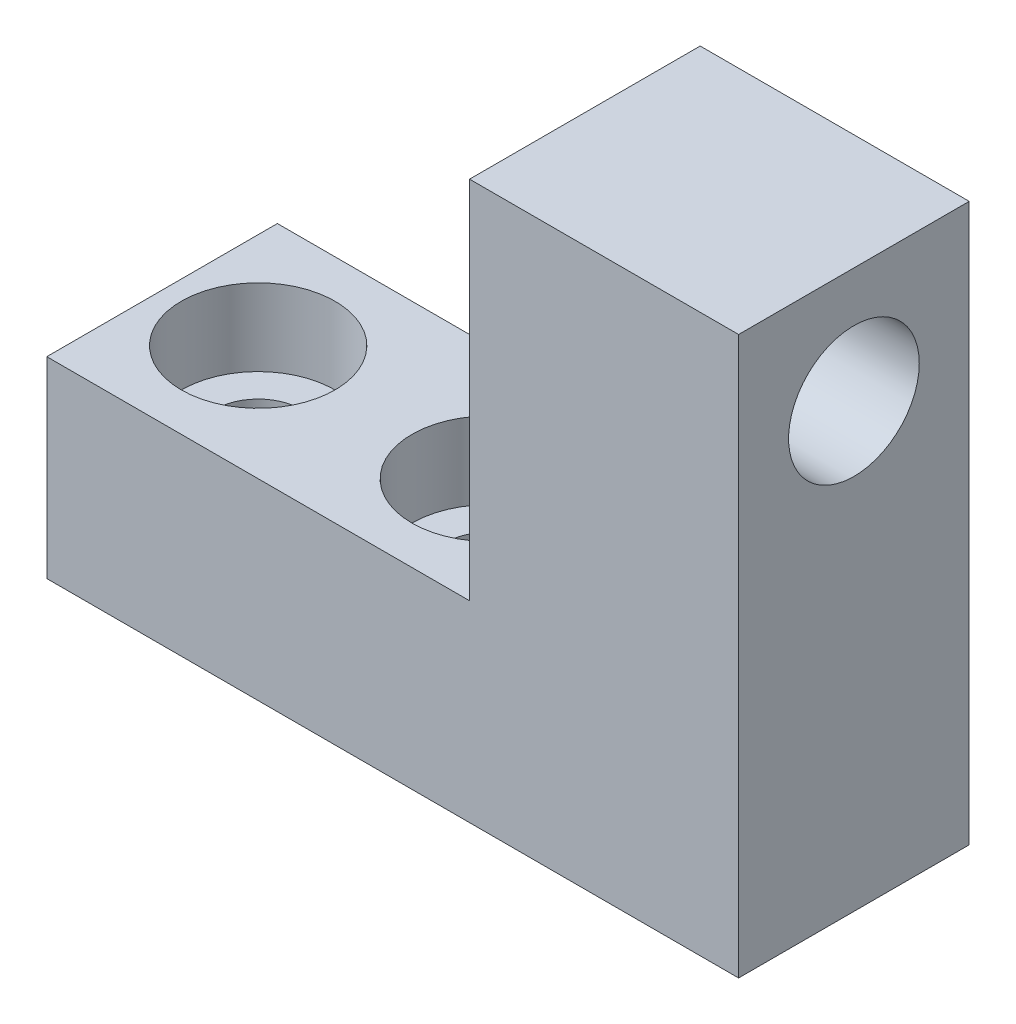
SolidWorks part; units mm, degrees
ref_plane "Front Plane" through (0, 0, 0) normal (0, 0, 1) x (1, 0, 0)
ref_plane "Top Plane" through (0, 0, 0) normal (0, 1, 0) x (1, 0, 0)
ref_plane "Right Plane" through (0, 0, 0) normal (1, 0, 0) x (0, 0, -1)
sketch "Sketch1" plane through (0, 0, 0) normal (0, 0, 1) x (1, 0, 0)
  line L1 (-8.2774, 3.0437) -> (27.7226, 3.0437)
  line L2 (-8.2774, 3.0437) -> (-8.2774, -6.9563)
  line L3 (-8.2774, -6.9563) -> (27.7226, -6.9563)
  line L4 (27.7226, 3.0437) -> (27.7226, -6.9563)
  dimension "D1" = 36
  dimension "D2" = 10
extrude "Boss-Extrude1" add sketch "Sketch1" along normal blind 12
sketch "Sketch2" plane through (0, 3.0437, 0) normal (0, 1, 0) x (1, 0, 0)
  line L0 (27.7226, 0) -> (-8.2774, 0) construction
  line L1 (27.7226, -12) -> (13.7226, -12)
  line L2 (27.7226, -12) -> (27.7226, 0)
  line L3 (27.7226, 0) -> (13.7226, 0)
  line L4 (13.7226, -12) -> (13.7226, 0)
  dimension "D1" = 14
extrude "Boss-Extrude2" add sketch "Sketch2" along normal blind 19
sketch "Sketch3" plane through (0, 3.0437, 0) normal (0, 1, 0) x (1, 0, 0)
  line L0 (-8.2774, -12) -> (-8.2774, 0) construction
  line L1 (27.7226, -12) -> (27.7226, 0) construction
  circle A0 centre (-3.2774, -6) radius 2.25
  circle A1 centre (8.7226, -6) radius 2.25
  point P6 (-8.2774, -6)
  dimension "D1" = 4.5
  dimension "D2" = 5
  dimension "D3" = 19
extrude "Cut-Extrude1" cut sketch "Sketch3" against normal through all
sketch "Sketch4" plane through (0, 3.0437, 0) normal (0, 1, 0) x (1, 0, 0)
  circle A0 centre (-3.2774, -6) radius 4
  circle A1 centre (8.7226, -6) radius 4
  dimension "D1" = 8
  dimension "D2" = 8
extrude "Cut-Extrude2" cut sketch "Sketch4" against normal blind 4
hole_wizard "M8 Tapped Hole1" positions "Sketch5" profile "Sketch6" tap size "M8" standard "ISO"
sketch "Sketch5" plane through (27.7226, 0, 0) normal (1, 0, 0) x (0, 0, -1)
  line L0 (-12, 22.0437) -> (0, 22.0437) construction
  point P0 (-6, 16.0437)
  dimension "D1" = 6
sketch "Sketch6" plane through (27.7226, 16.0437, 6) normal (0, 1, 0) x (0, 0, -1)
  line L0 (0, 0) -> (0, 21.7929)
  line L1 (0, 21.7929) -> (3.4, 19.75)
  line L2 (3.4, 19.75) -> (3.4, 0)
  line L5 (3.4, 0) -> (0, 0)
  line L10 (0, 21.7929) -> (-3.4, 19.75) construction
  line L11 (0, -6.35) -> (0, 107.95) construction
  dimension "Tap Drill Dia." = 6.8
  dimension "Tap Drill Depth" = 19.75
  dimension "Drill Angle" = 118
cosmetic thread "Hole Thread1" parameters "D1"=14, "D2"=8
